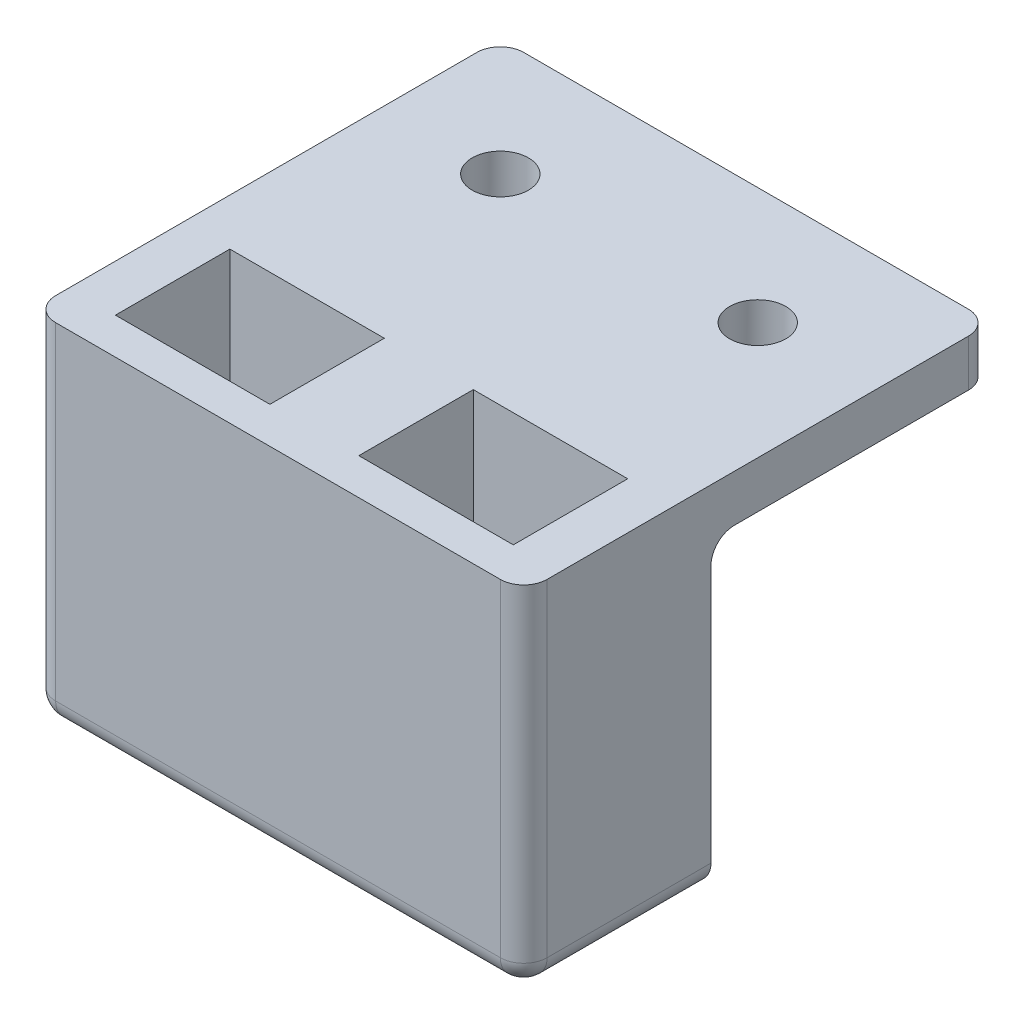
SolidWorks part; units mm, degrees
ref_plane "Front Plane" through (0, 0, 0) normal (0, 0, 1) x (1, 0, 0)
ref_plane "Top Plane" through (0, 0, 0) normal (0, 1, 0) x (1, 0, 0)
ref_plane "Right Plane" through (0, 0, 0) normal (1, 0, 0) x (0, 0, -1)
sketch "Sketch1" plane through (0, 0, 0) normal (0, 1, 0) x (1, 0, 0)
  line L1 (0, 0) -> (21, 0)
  line L2 (0, 0) -> (0, 8)
  line L3 (0, 8) -> (21, 8)
  line L4 (21, 0) -> (21, 8)
  dimension "D1" = 8
  dimension "D2" = 21
extrude "mainBody" add sketch "Sketch1" along normal blind 15
sketch "Sketch3" plane through (0, 15, 0) normal (0, 1, 0) x (1, 0, 0)
  line L0 (10.5, 8) -> (10.5, 0) construction
  line L1 (2, 1.555) -> (8.6, 1.555)
  line L2 (2, 1.555) -> (2, 6.445)
  line L3 (2, 6.445) -> (8.6, 6.445)
  line L4 (8.6, 1.555) -> (8.6, 6.445)
  line L5 (21, 8) -> (0, 8) construction
  line L6 (0, 0) -> (21, 0) construction
  point P10 (8.6, 4)
  point P11 (10.5, 4)
  dimension "D1" = 6.6
  dimension "D2" = 4.89
  dimension "D3" = 8.5
extrude "QRDClearance" cut sketch "Sketch3" against normal offset from surface (12 mm away) 3 up to face at (10.5, 0, -4)
sketch "Sketch4" plane through (0, 3, 0) normal (0, 1, 0) x (1, 0, 0)
  line L0 (8.6, 6.445) -> (2, 6.445) construction
  line L1 (3, 6.445) -> (7.6, 6.445)
  line L2 (3, 6.445) -> (3, 1.555)
  line L3 (3, 1.555) -> (7.6, 1.555)
  line L4 (7.6, 6.445) -> (7.6, 1.555)
  line L5 (2, 1.555) -> (8.6, 1.555) construction
  line L6 (2, 6.445) -> (2, 1.555) construction
  line L7 (8.6, 1.555) -> (8.6, 6.445) construction
  dimension "D1" = 1
  dimension "D2" = 1
extrude "visionTunnel" cut sketch "Sketch4" against normal up to surface (3 mm away) up to face at (10.5, 0, -4)
ref_plane "midWidthPlane" through (10.5, 0, 0) normal (-1, 0, 0) x (0, 0, 1)
mirror "socketMirror" about plane through (10.5, 0, 0) normal (-1, 0, 0) of "visionTunnel", "QRDClearance"
fillet "Fillet1" radius 1 5 edges at (0, 7.5, 0) (21, 7.5, 0) (0, 0, -4) (21, 0, -4) (10.5, 0, 0)
sketch "Sketch5" plane through (0, 0, -8) normal (0, 0, -1) x (-1, 0, 0)
  line L0 (0, 15) -> (0, 1) construction
  line L1 (-21, 15) -> (0, 15)
  line L2 (-21, 15) -> (-21, 13)
  line L3 (-21, 13) -> (0, 13)
  line L4 (0, 15) -> (0, 13)
  dimension "D1" = 2
extrude "fasteningBracket" add sketch "Sketch5" along normal blind 12
fillet "Fillet2" radius 1 3 edges at (0, 14, -20) (21, 14, -20)
hole_wizard "M2 Clearance Hole1" positions "3DSketch1" profile "Sketch6" hole size "M2" standard "ISO"
sketch3d "3DSketch1"
  line L0 (1, 15, -20) -> (20, 15, -20) construction
  line L1 (21, 15, -1) -> (21, 15, -19) construction
  line L2 (0, 15, -19) -> (0, 15, -1) construction
  point P0 (5, 15, -15)
  point P2 (16, 15, -15)
  dimension "D1" = 5
  dimension "D2" = 5
  dimension "D3" = 5
sketch "Sketch6" plane through (5, 15, -15) normal (1, 0, 0) x (0, 0, 1)
  line L0 (0, 0) -> (0, 2.72)
  line L1 (0, 2.72) -> (1.2, 1.999)
  line L2 (1.2, 1.999) -> (1.2, 0)
  line L5 (1.2, 0) -> (0, 0)
  line L10 (0, 2.72) -> (-1.2, 1.999) construction
  line L11 (0, -6.35) -> (0, 107.95) construction
  dimension "Hole Dia." = 2.4
  dimension "Hole Depth" = 1.999
  dimension "Drill Angle" = 118
